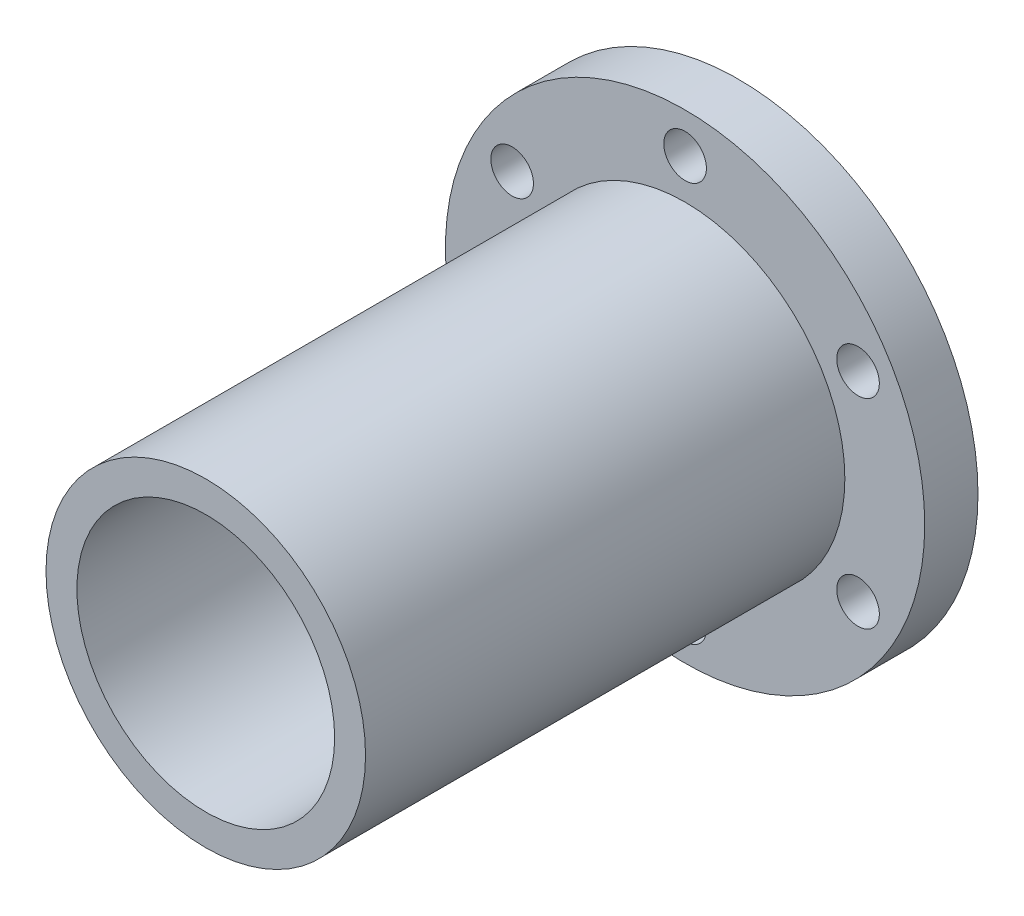
SolidWorks part; units mm, degrees
ref_plane "Front Plane" through (0, 0, 0) normal (0, 0, 1) x (1, 0, 0)
ref_plane "Top Plane" through (0, 0, 0) normal (0, 1, 0) x (1, 0, 0)
ref_plane "Right Plane" through (0, 0, 0) normal (1, 0, 0) x (0, 0, -1)
sketch "Sketch1" plane through (0, 0, 0) normal (0, 0, 1) x (1, 0, 0)
  circle A0 centre (0, 0) radius 22.5
  dimension "D1" = 45
extrude "Boss-Extrude1" add sketch "Sketch1" along normal blind 5
sketch "Sketch2" plane through (0, 0, 5) normal (0, 0, 1) x (1, 0, 0)
  circle A0 centre (0, 0) radius 15
  circle A1 centre (0, 0) radius 12.1
  dimension "D1" = 30
  dimension "D2" = 24.2
extrude "Boss-Extrude2" add sketch "Sketch2" along normal blind 45
sketch "Sketch3" plane through (0, 0, 5) normal (0, 0, 1) x (1, 0, 0)
  circle A0 centre (0, 18.75) radius 2
  circle A1 centre (16.238, 9.375) radius 2
  circle A2 centre (16.238, -9.375) radius 2
  circle A3 centre (0, -18.75) radius 2
  circle A4 centre (-16.238, -9.375) radius 2
  circle A5 centre (-16.238, 9.375) radius 2
  circle A6 centre (0, 0) radius 18.75 construction
  point P15 (0, 0)
  dimension "D1" = 4
  dimension "D3" = 37.5
  dimension "D2" = 6
extrude "Cut-Extrude1" cut sketch "Sketch3" against normal blind 5
